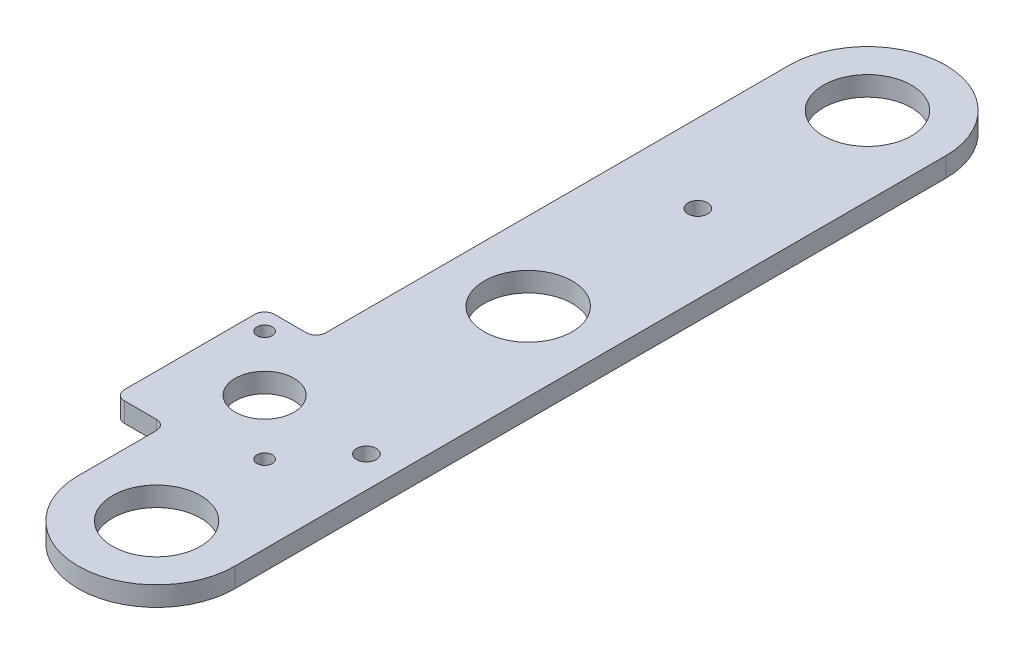
SolidWorks part; units mm, degrees
material "Acrylic (Medium-high impact)"
ref_plane "Front Plane" through (0, 0, 0) normal (0, 0, 1) x (1, 0, 0)
ref_plane "Top Plane" through (0, 0, 0) normal (0, 1, 0) x (1, 0, 0)
ref_plane "Right Plane" through (0, 0, 0) normal (1, 0, 0) x (0, 0, -1)
sketch "Sketch1" plane through (0, 0, 0) normal (0, 1, 0) x (1, 0, 0)
  line L0 (-352.425, 406.4) -> (-352.425, 488.95) construction
  line L1 (-352.425, -406.4) -> (352.425, -406.4) construction
  line L2 (-352.425, -406.4) -> (-352.425, 406.4) construction
  line L3 (-352.425, 406.4) -> (352.425, 406.4) construction
  line L4 (352.425, -406.4) -> (352.425, 406.4) construction
  line L5 (-352.425, -406.4) -> (352.425, 406.4) construction
  line L6 (-352.425, 406.4) -> (352.425, -406.4) construction
  line L7 (-434.975, -488.95) -> (434.975, -488.95) construction
  line L8 (-434.975, -488.95) -> (-434.975, 488.95) construction
  line L9 (-434.975, 488.95) -> (434.975, 488.95) construction
  line L10 (434.975, -488.95) -> (434.975, 488.95) construction
  line L11 (-434.975, -488.95) -> (434.975, 488.95) construction
  line L12 (-434.975, 488.95) -> (434.975, -488.95) construction
  line L13 (352.425, 406.4) -> (352.425, 488.95) construction
  line L14 (200.025, 488.95) -> (200.025, 406.4) construction
  line L15 (-200.025, 488.95) -> (-200.025, 406.4) construction
  line L16 (-352.425, 447.675) -> (-200.025, 447.675) construction
  line L17 (0, 0) -> (0, 262.3775) construction
  line L18 (200.025, 447.675) -> (352.425, 447.675) construction
  line L19 (-575.6491, 254) -> (705.9623, 254) construction
  line L20 (-139.7, 342.9) -> (139.7, 342.9) construction
  line L21 (-139.7, 342.9) -> (-139.7, 673.1) construction
  line L22 (-139.7, 673.1) -> (139.7, 673.1) construction
  line L23 (139.7, 342.9) -> (139.7, 673.1) construction
  line L24 (-139.7, 342.9) -> (139.7, 673.1) construction
  line L25 (-139.7, 673.1) -> (139.7, 342.9) construction
  line L26 (-165.1, 342.9) -> (165.1, 342.9) construction
  line L27 (-165.1, 342.9) -> (-165.1, 622.3) construction
  line L28 (-165.1, 622.3) -> (165.1, 622.3) construction
  line L29 (165.1, 342.9) -> (165.1, 622.3) construction
  line L30 (-165.1, 342.9) -> (165.1, 622.3) construction
  line L31 (-165.1, 622.3) -> (165.1, 342.9) construction
  line L32 (-498.863, 292.1) -> (699.369, 292.1) construction
  line L33 (-233.4867, 576.3867) -> (0, 809.8733) construction
  line L34 (-233.4867, 576.3867) -> (0, 342.9) construction
  line L35 (0, 809.8733) -> (233.4867, 576.3867) construction
  line L36 (0, 342.9) -> (233.4867, 576.3867) construction
  line L37 (0, 342.9) -> (0, 809.8733) construction
  line L38 (-210.82, 548.0346) -> (-210.82, 438.0272)
  line L39 (-210.82, 438.0272) -> (-210.82, 317.5)
  line L40 (210.82, 548.0346) -> (210.82, 438.0272)
  line L41 (210.82, 438.0272) -> (210.82, 317.5)
  line L42 (-210.82, 317.5) -> (210.82, 317.5)
  line L43 (-160.02, 548.0346) -> (160.02, 548.0346) construction
  line L44 (-210.82, 317.5) -> (-241.4506, 434.07) construction
  line L45 (-241.4506, 434.07) -> (-269.4077, 540.4656) construction
  line L46 (210.82, 317.5) -> (241.4506, 434.07) construction
  line L47 (241.4506, 434.07) -> (269.4077, 540.4656) construction
  line L48 (-434.975, 488.95) -> (-269.4077, 540.4656) construction
  line L49 (269.4077, 540.4656) -> (434.975, 488.95) construction
  line L50 (-269.4077, 540.4656) -> (-233.4867, 576.3867) construction
  line L51 (-434.975, 273.05) -> (20.0901, 273.05) construction
  line L52 (-210.82, 304.8) -> (210.82, 304.8) construction
  line L53 (-210.82, 304.8) -> (-210.82, 330.2) construction
  line L54 (-210.82, 330.2) -> (210.82, 330.2) construction
  line L55 (210.82, 304.8) -> (210.82, 330.2) construction
  circle A0 centre (-210.82, 548.0346) radius 50.8
  circle A1 centre (210.82, 548.0346) radius 50.8
  circle A2 centre (210.82, 438.0272) radius 50.8
  circle A3 centre (-210.82, 438.0272) radius 50.8
  circle A4 centre (269.4077, 540.4656) radius 50.8 construction
  circle A5 centre (241.4506, 434.07) radius 50.8 construction
  circle A6 centre (-241.4506, 434.07) radius 50.8 construction
  circle A7 centre (-269.4077, 540.4656) radius 50.8 construction
  point P0 (0, 0)
  point P6 (0, 0)
  point P22 (0, 508)
  point P28 (0, 482.6)
  point P67 (0, 317.5)
  point P68 (210.82, 317.5)
  dimension "D10" = 101.6
  dimension "D1" = 812.8
  dimension "D2" = 704.85
  dimension "D3" = 82.55
  dimension "D4" = 82.55
  dimension "D5" = 152.4
  dimension "D6" = 279.4
  dimension "D7" = 330.2
  dimension "D8" = 152.4
  dimension "D9" = 38.1
  dimension "D11" = 320.04
  dimension "D12" = 25.4
  dimension "D13" = 25.4
  dimension "D14" = 110.0074
  dimension "D15" = 25.4
  dimension "D16" = 19.05
sketch "Sketch3" plane through (0, 0, 0) normal (0, 1, 0) x (1, 0, 0)
  line L0 (-249.7355, 346.0124) -> (-239.395, 346.0124)
  line L1 (-252.9105, 349.1874) -> (-252.9105, 391.4584)
  line L2 (-210.82, 548.0346) -> (-210.82, 317.5) construction
  line L3 (-185.42, 548.0346) -> (-185.42, 317.5)
  line L7 (-210.82, 370.3229) -> (-228.6, 370.3229) construction
  line L10 (-246.5605, 352.3624) -> (-210.6395, 388.2834) construction
  line L11 (-228.6, 370.3229) -> (-210.82, 438.0272) construction
  line L12 (-246.5605, 352.3624) -> (-210.6395, 352.3624) construction
  line L13 (-246.5605, 352.3624) -> (-246.5605, 388.2834) construction
  line L14 (-246.5605, 388.2834) -> (-210.6395, 388.2834) construction
  line L15 (-210.6395, 352.3624) -> (-210.6395, 388.2834) construction
  line L16 (-210.82, 548.0346) -> (-210.82, 438.0272)
  line L17 (-210.82, 438.0272) -> (-228.6, 370.3229)
  line L18 (-210.82, 370.3229) -> (210.82, 370.3229) construction
  line L19 (210.82, 370.3229) -> (228.6, 370.3229) construction
  line L20 (210.82, 438.0272) -> (210.82, 317.5) construction
  line L21 (210.82, 438.0272) -> (210.82, 317.5) construction
  line L22 (-236.22, 397.8084) -> (-236.22, 548.0346)
  line L24 (-249.7355, 394.6334) -> (-239.395, 394.6334)
  line L25 (-252.9105, 346.0124) -> (-252.9105, 394.6334) construction
  line L26 (-252.9105, 394.6334) -> (-210.6395, 394.6334) construction
  line L27 (-236.22, 342.8374) -> (-236.22, 317.5)
  line L28 (-252.9105, 346.0124) -> (-210.6395, 346.0124) construction
  circle A8 centre (-210.82, 548.0346) radius 14.2748
  circle A9 centre (-210.82, 438.0272) radius 14.2748
  circle A10 centre (-210.82, 317.5) radius 14.2748
  arc A11 (-185.42, 548.0346) -> (-236.22, 548.0346) centre (-210.82, 548.0346) ccw
  arc A12 (-236.22, 317.5) -> (-185.42, 317.5) centre (-210.82, 317.5) ccw
  circle A13 centre (-228.6, 370.3229) radius 9.525
  circle A14 centre (-228.6, 370.3229) radius 25.4 construction
  arc A19 (-239.395, 346.0124) -> (-236.22, 342.8374) centre (-239.395, 342.8374) cw
  arc A20 (-249.7355, 346.0124) -> (-252.9105, 349.1874) centre (-249.7355, 349.1874) cw
  arc A21 (-252.9105, 391.4584) -> (-249.7355, 394.6334) centre (-249.7355, 391.4584) cw
  arc A22 (-239.395, 394.6334) -> (-236.22, 397.8084) centre (-239.395, 397.8084) ccw
  circle A24 centre (-246.5605, 388.2834) radius 2.4892
  circle A25 centre (-210.6395, 352.3624) radius 2.4892
  circle A26 centre (-210.82, 493.0309) radius 3.175
  circle A27 centre (-195.58, 370.3229) radius 3.175
  dimension "D1" = 28.5496
  dimension "D3" = 19.05
  dimension "D4" = 4.9784
  dimension "D7" = 50.8
  dimension "D9" = 10.16
  dimension "D12" = 3.175
  dimension "D8" = 6.35
  dimension "D2" = 50.8
  dimension "D5" = 457.2
  dimension "D6" = 70
  dimension "D11" = 6.35
extrude "Boss-Extrude1" add sketch "Sketch3" along normal blind 6.35
